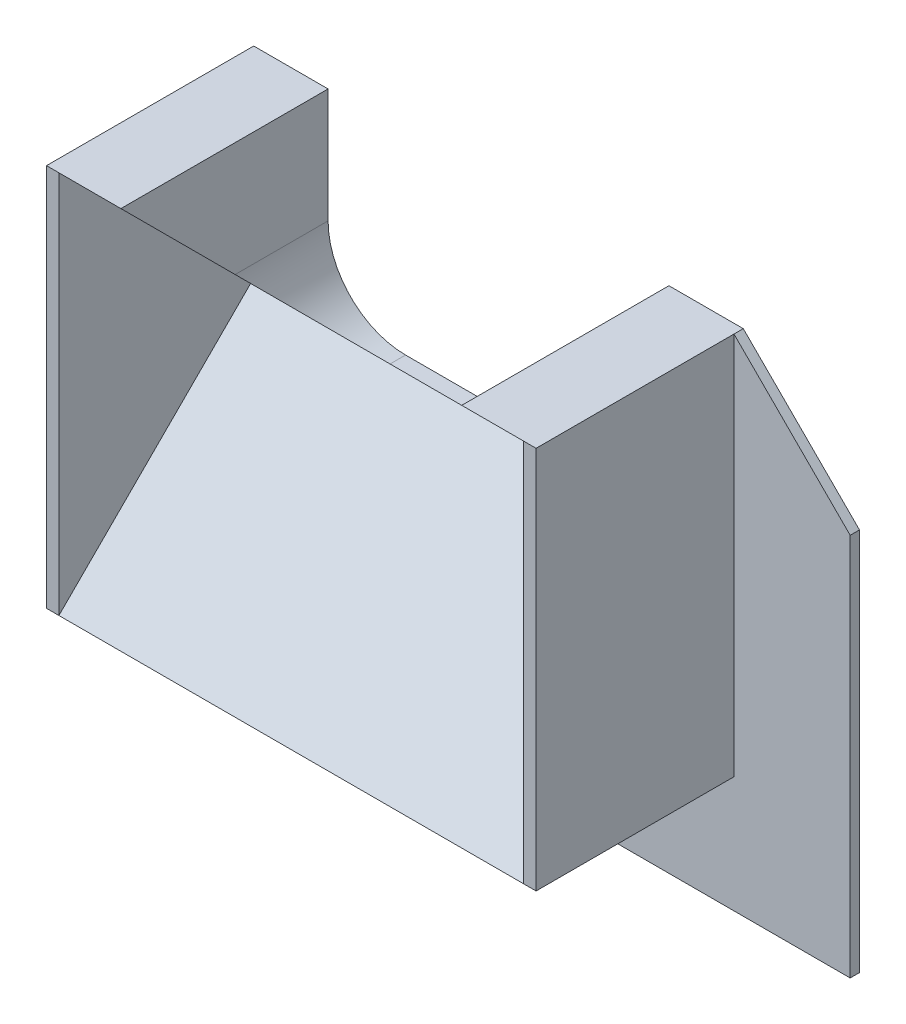
SolidWorks part; units mm, degrees
ref_plane "Front Plane" through (0, 0, 0) normal (0, 0, 1) x (1, 0, 0)
ref_plane "Top Plane" through (0, 0, 0) normal (0, 1, 0) x (1, 0, 0)
ref_plane "Right Plane" through (0, 0, 0) normal (1, 0, 0) x (0, 0, -1)
sketch "Sketch1" plane through (0, 0, 0) normal (1, 0, 0) x (0, 0, -1)
  line L0 (-24.7487, 24.7487) -> (0, 0)
  line L1 (0, 0) -> (-24.7487, -24.7487)
  line L2 (-24.7487, -24.7487) -> (2, -24.7487)
  line L3 (2, -24.7487) -> (2, 24.7487)
  line L4 (2, 24.7487) -> (-24.7487, 24.7487)
  dimension "D1" = 2
  dimension "D2" = 35
extrude "Boss-Extrude1" add sketch "Sketch1" along normal blind 60
sketch "Sketch2" plane through (0, 0, -2) normal (0, 0, -1) x (-1, 0, 0)
  line L0 (-60, 24.7487) -> (0, 24.7487) construction
  line L1 (-52, 0) -> (-8, 0)
  line L2 (-52, 0) -> (-52, 24.7487)
  line L3 (-52, 24.7487) -> (-8, 24.7487)
  line L4 (-8, 0) -> (-8, 24.7487)
  line L5 (-30, 24.7487) -> (-30, 0) construction
  line L6 (-52, 12.3744) -> (-8, 12.3744) construction
  line L7 (0, -24.7487) -> (0, 24.7487) construction
  point P0 (-30, 12.3744)
  point P6 (0, 0)
  dimension "D1" = 8
extrude "Cut-Extrude1" cut sketch "Sketch2" against normal through all
fillet "Fillet1" radius 10 2 edges at (8, 0, -1) (52, 0, -1)
ref_plane "Plane1" through (30, 0, 0) normal (-1, 0, 0) x (0, 0, 1)
sketch "Sketch5" plane through (0, 0, 0) normal (-1, 0, 0) x (0, 0, 1)
  line L1 (24.7487, 24.7487) -> (-2, 24.7487)
  line L2 (24.7487, 24.7487) -> (24.7487, -24.7487)
  line L3 (24.7487, -24.7487) -> (-2, -24.7487)
  line L4 (-2, 24.7487) -> (-2, -24.7487)
  line L5 (11.3744, -24.7487) -> (11.3744, 24.7487) construction
  line L6 (24.7487, 0) -> (-2, 0) construction
  point P324 (11.3744, 0)
extrude "Boss-Extrude3" add sketch "Sketch5" along normal blind 1.6
mirror "Mirror1" about plane through (30, 0, 0) normal (-1, 0, 0) of "Boss-Extrude3"
sketch "Sketch6" plane through (0, 0, -2) normal (0, 0, -1) x (-1, 0, 0)
  line L0 (1.6, 24.7487) -> (16.6, 9.7487)
  line L1 (16.6, 9.7487) -> (16.6, -39.7487)
  line L2 (16.6, -39.7487) -> (-76.6, -39.7487)
  line L3 (-76.6, -39.7487) -> (-76.6, 9.7487)
  line L4 (-76.6, 9.7487) -> (-61.6, 24.7487)
  line L5 (-61.6, 24.7487) -> (-61.6, -24.7487)
  line L6 (-61.6, -24.7487) -> (1.6, -24.7487)
  line L7 (1.6, -24.7487) -> (1.6, 24.7487)
  line L8 (-76.6, -24.7487) -> (-61.6, -24.7487) construction
  line L9 (-61.6, -39.7487) -> (-61.6, -24.7487) construction
  dimension "D1" = 15
extrude "Boss-Extrude4" add sketch "Sketch6" against normal blind 1.2
